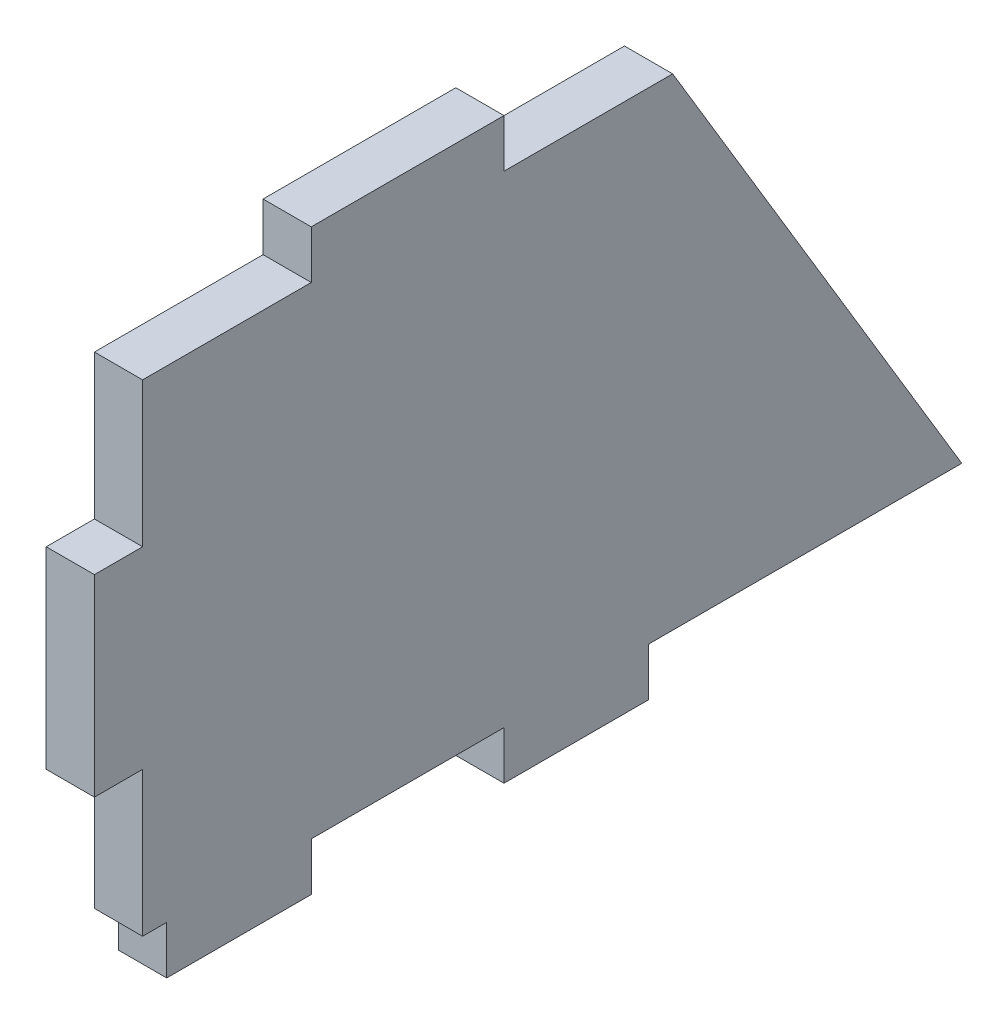
SolidWorks part; units mm, degrees
ref_plane "Plan de face" through (0, 0, 0) normal (0, 0, 1) x (1, 0, 0)
ref_plane "Plan de dessus" through (0, 0, 0) normal (0, 1, 0) x (1, 0, 0)
ref_plane "Plan de droite" through (0, 0, 0) normal (1, 0, 0) x (0, 0, -1)
sketch "Esquisse1" plane through (0, 0, 0) normal (1, 0, 0) x (0, 0, -1)
  line L0 (55, 0) -> (85, -50)
  line L1 (0, 0) -> (17.5, 0)
  line L2 (-5, -15) -> (-5, -35)
  line L6 (2.5, -55) -> (17.5, -55)
  line L7 (0, -50) -> (2.5, -50)
  line L8 (2.5, -50) -> (2.5, -55)
  line L9 (17.5, -55) -> (17.5, -50)
  line L10 (17.5, -50) -> (37.5, -50)
  line L11 (37.5, -50) -> (37.5, -55)
  line L12 (52.5, -55) -> (52.5, -50)
  line L13 (52.5, -50) -> (85, -50)
  line L14 (37.5, -55) -> (52.5, -55)
  line L15 (0, 0) -> (0, -15)
  line L16 (0, -15) -> (-5, -15)
  line L17 (-5, -35) -> (0, -35)
  line L18 (0, -35) -> (0, -50)
  line L19 (27.5, -50) -> (27.5, -6.4869) construction
  line L20 (-5, -25) -> (23.79, -25) construction
  line L21 (55, 0) -> (55, -50) construction
  line L22 (55, -25) -> (93.7956, -25) construction
  line L23 (17.5, 0) -> (17.5, 5)
  line L24 (17.5, 5) -> (37.5, 5)
  line L25 (37.5, 5) -> (37.5, 0)
  line L26 (37.5, 0) -> (55, 0)
  dimension "D2" = 60
  dimension "D3" = 5
  dimension "D4" = 5
  dimension "D6" = 20
  dimension "D7" = 15
  dimension "D8" = 32.5
  dimension "D10" = 30
  dimension "D5" = 20
  dimension "D9" = 15
  dimension "D11" = 5
  dimension "D12" = 50
extrude "Boss.-Extru.1" add sketch "Esquisse1" along normal blind 5
equation "\"D4@Esquisse1\"=\"D3@Esquisse1\""
equation "\"D8@Esquisse1\"=175-142.5"
equation "\"D10@Esquisse1\"=\"D2@Esquisse1\"/2"
equation "\"D5@Esquisse1\"=\"D6@Esquisse1\""
equation "\"D9@Esquisse1\"=\"D7@Esquisse1\""
equation "\"D11@Esquisse1\"=\"D3@Esquisse1\""
